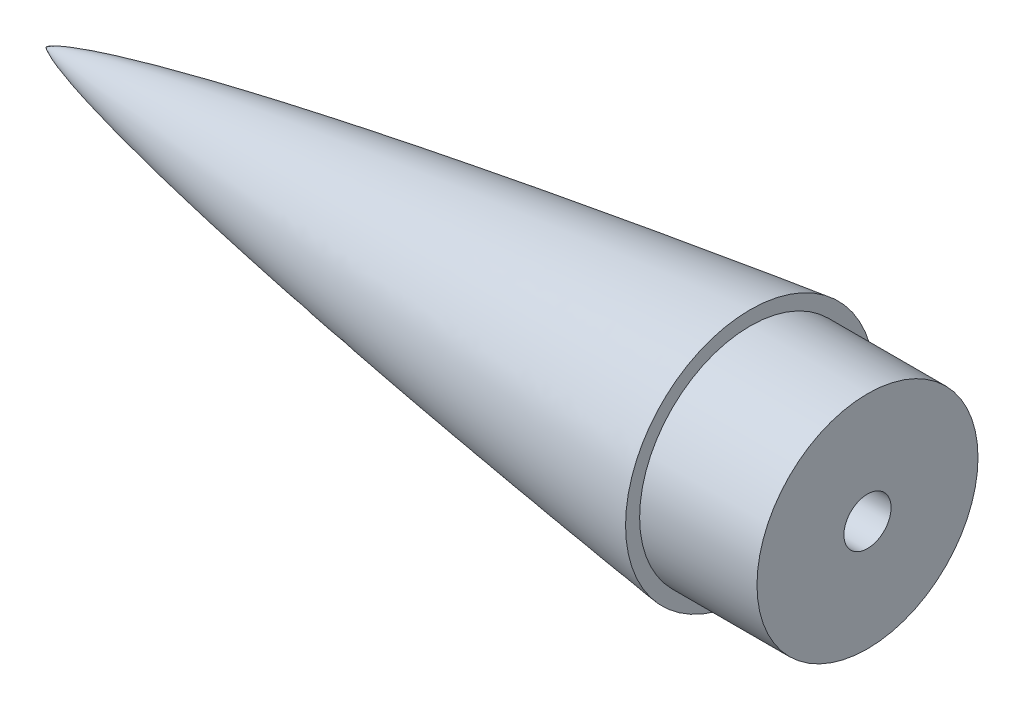
SolidWorks part; units mm, degrees
material "1060 Alloy"
ref_plane "Front Plane" through (0, 0, 0) normal (0, 0, 1) x (1, 0, 0)
ref_plane "Top Plane" through (0, 0, 0) normal (0, 1, 0) x (1, 0, 0)
ref_plane "Right Plane" through (0, 0, 0) normal (1, 0, 0) x (0, 0, -1)
sketch "Sketch1" plane through (0, 0, 0) normal (0, 0, 1) x (1, 0, 0)
  line L0 (609.7035, 49.5425) -> (0, 49.5425) construction
  line L1 (0, 0) -> (609.7035, 0) construction
  line L2 (609.7035, 0) -> (609.7035, 49.5425) construction
  line L4 (0, 0) -> (4.2432, 0)
  line L5 (609.7035, 49.5425) -> (609.7035, 48.0185)
  line L6 (76.2, 49.5425) -> (76.2, 0)
  line L7 (76.2, 0) -> (0, 0)
  spline S0 degree 4 poles (0, 0) (0.0026, 0.0056) (0.0087, 0.0163) (0.0248, 0.0349) (0.0614, 0.0678) (0.1157, 0.1081) (0.188, 0.1546) (0.2908, 0.214) (0.4142, 0.2786) (0.5588, 0.3483) (0.7247, 0.4227) (0.9641, 0.524) (1.3347, 0.6697) (1.9693, 0.8979) (3.107, 1.2651) (5.1421, 1.8472) (8.9246, 2.7936) (16.0543, 4.3335) (28.7745, 6.6819) (49.7554, 9.994) (78.1202, 13.8444) (112.1347, 17.9128) (149.32, 21.9008) (186.5406, 25.5414) (223.7883, 28.8926) (261.0579, 31.9909) (298.3459, 34.8583) (335.6499, 37.5082) (372.9683, 39.947) (410.2999, 42.1753) (447.6438, 44.1872) (484.9994, 45.9696) (517.6955, 47.3072) (545.7276, 48.2682) (568.3263, 48.8964) (583.5347, 49.2341) (596.0246, 49.4397) (603.8409, 49.5199) (607.7493, 49.5425) (609.7035, 49.5425) knots 0 0 0 0 0 0.00004 0.00008 0.00016 0.000321 0.000481 0.000642 0.000936 0.00123 0.001529 0.001829 0.002633 0.003829 0.005933 0.009636 0.016455 0.029289 0.053563 0.094103 0.155164 0.216224 0.277285 0.338345 0.399406 0.460466 0.521526 0.582587 0.643647 0.704708 0.765768 0.826829 0.887889 0.918419 0.948949 0.974475 0.987237 1 1 1 1 1 construction
  spline S1 degree 4 poles (0, 0) (0.0026, 0.0056) (0.0087, 0.0163) (0.0248, 0.0349) (0.0614, 0.0678) (0.1157, 0.1081) (0.188, 0.1546) (0.2908, 0.214) (0.4142, 0.2786) (0.5588, 0.3483) (0.7247, 0.4227) (0.9641, 0.524) (1.3347, 0.6697) (1.9693, 0.8979) (3.107, 1.2651) (5.1421, 1.8472) (8.9246, 2.7936) (16.0543, 4.3335) (28.7745, 6.6819) (49.7554, 9.994) (78.1202, 13.8444) (112.1347, 17.9128) (149.32, 21.9008) (186.5406, 25.5414) (223.7883, 28.8926) (261.0579, 31.9909) (298.3459, 34.8583) (335.6499, 37.5082) (372.9683, 39.947) (410.2999, 42.1753) (447.6438, 44.1872) (484.9994, 45.9696) (517.6955, 47.3072) (545.7276, 48.2682) (568.3263, 48.8964) (583.5347, 49.2341) (596.0246, 49.4397) (603.8409, 49.5199) (607.7493, 49.5425) (609.7035, 49.5425) knots 0 0 0 0 0 0.00004 0.00008 0.00016 0.000321 0.000481 0.000642 0.000936 0.00123 0.001529 0.001829 0.002633 0.003829 0.005933 0.009636 0.016455 0.029289 0.053563 0.094103 0.155164 0.216224 0.277285 0.338345 0.399406 0.460466 0.521526 0.582587 0.643647 0.704708 0.765768 0.826829 0.887889 0.918419 0.948949 0.974475 0.987237 1 1 1 1 1
  spline S2 degree 1 poles (1.0385, -1.1154) (609.7035, 48.0185) knots 0 0 1 1 construction
  spline S3 degree 3 poles (1.0385, -1.1154) (1.0989, -1.083) (1.2128, -1.0279) (1.5232, -0.8922) (2.1055, -0.6677) (3.0053, -0.366) (4.1131, -0.0333) (5.6153, 0.3841) (7.5186, 0.8678) (10.5921, 1.5877) (14.4643, 2.4134) (19.1367, 3.3301) (23.8239, 4.1916) (30.089, 5.283) (37.9399, 6.5629) (47.381, 7.9992) (58.5528, 9.6059) (69.7401, 11.1192) (82.378, 12.7438) (96.4664, 14.476) (113.7321, 16.4844) (132.7363, 18.5735) (158.0914, 21.2218) (189.8103, 24.3062) (227.9026, 27.7085) (266.0186, 30.8488) (304.1542, 33.7496) (342.3067, 36.4242) (393.1966, 39.6957) (444.1134, 42.5278) (495.0523, 44.8735) (533.2675, 46.3537) (565.1178, 47.3188) (590.6059, 47.8413) (603.3361, 48.0185) (609.7035, 48.0185) knots 0.000645 0.000645 0.000645 0.000645 0.001133 0.001621 0.002597 0.004549 0.0065 0.008452 0.012356 0.01626 0.024067 0.031875 0.039682 0.04749 0.063105 0.078719 0.094334 0.118452 0.134067 0.156794 0.188024 0.219254 0.250484 0.312943 0.375403 0.437863 0.500322 0.562782 0.625242 0.750161 0.812621 0.875081 0.93754 0.96877 1 1 1 1 only from (76.2, 11.9477) to (609.7035, 48.0185)
  dimension "D1" = 1.524
  dimension "D2" = 76.2
revolve "Revolve1" add sketch "Sketch1" angle 360 about L1
sketch "Sketch5" plane through (76.2, 0, 0) normal (1, 0, 0) x (0, 0, -1)
  circle A0 centre (0, 0) radius 11.9603
  circle A1 centre (0, 0) radius 13.4843 construction
  dimension "D1" = 1.524
extrude "Boss-Extrude1" add sketch "Sketch5" along normal blind 12.7
sketch "Sketch7" plane through (88.9, 0, 0) normal (1, 0, 0) x (0, 0, -1)
  point P0 (0, 0)
hole_wizard "1/4-20 Tapped Hole2" positions "Sketch7" profile "Sketch8" tap size "1/4-20" standard "ANSI Inch"
sketch "Sketch8" plane through (88.9, 0, 0) normal (0, 1, 0) x (0, 0, -1)
  line L0 (0, 0) -> (0, 50.8)
  line L1 (0, 50.8) -> (2.5527, 49.2662)
  line L2 (2.5527, 49.2662) -> (2.5527, 0)
  line L5 (2.5527, 0) -> (0, 0)
  line L10 (0, 50.8) -> (-2.5527, 49.2662) construction
  line L11 (0, -6.35) -> (0, 107.95) construction
  dimension "Tap Drill Dia." = 5.1054
  dimension "Tap Drill Depth" = 50.8
  dimension "Drill Angle" = 118
